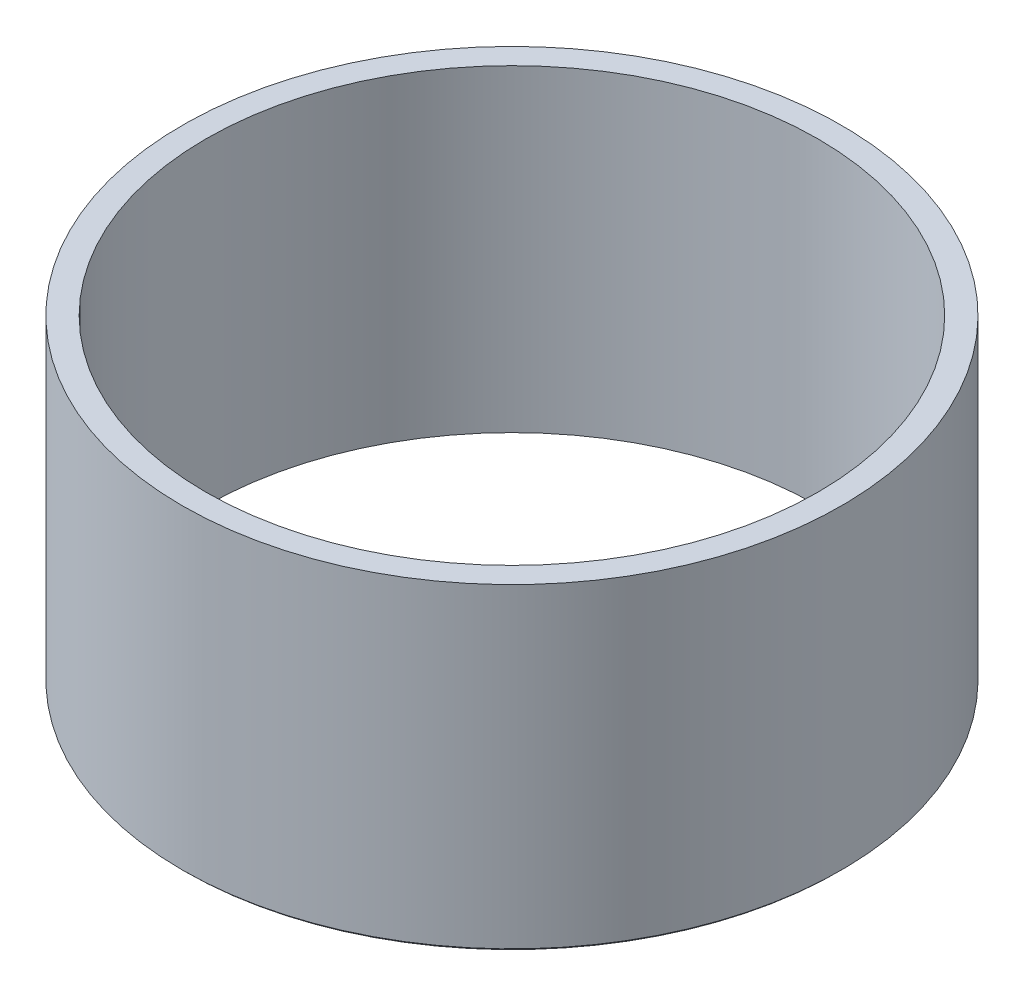
SolidWorks part; units mm, degrees
material "Aleación 1060"
ref_plane "Alzado" through (0, 0, 0) normal (0, 0, 1) x (1, 0, 0)
ref_plane "Planta" through (0, 0, 0) normal (0, 1, 0) x (1, 0, 0)
ref_plane "Vista lateral" through (0, 0, 0) normal (1, 0, 0) x (0, 0, -1)
sketch "Croquis1" plane through (0, 0, 0) normal (0, 1, 0) x (1, 0, 0)
  circle A0 centre (0, 0) radius 14
  circle A1 centre (0, 0) radius 13
  dimension "D1" = 28
  dimension "D2" = 1
extrude "Saliente-Extruir1" add sketch "Croquis1" along normal blind 13.5
chamfer "Chaflán1" distance 0.1 angle 45 1 edges at (0, 0, 14)
